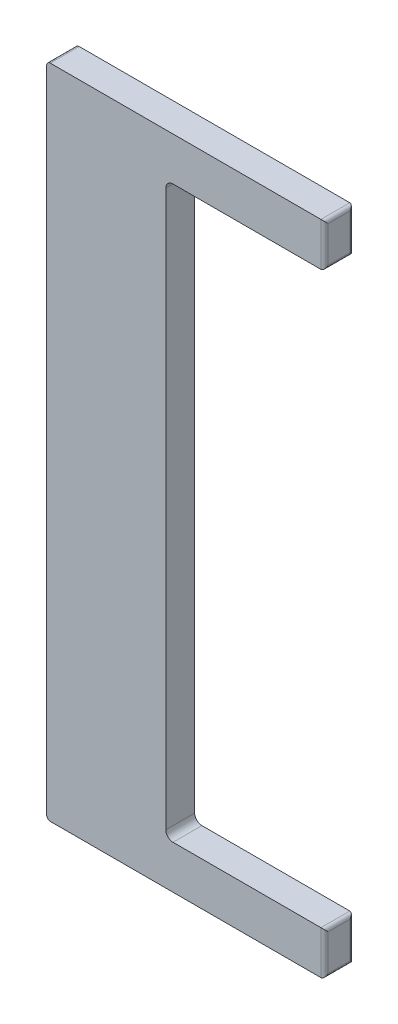
SolidWorks part; units mm, degrees
material "POLYURETHANE (11671)"
ref_plane "Front Plane" through (0, 0, 0) normal (0, 0, 1) x (1, 0, 0)
ref_plane "Top Plane" through (0, 0, 0) normal (0, 1, 0) x (1, 0, 0)
ref_plane "Right Plane" through (0, 0, 0) normal (1, 0, 0) x (0, 0, -1)
sketch "Sketch1" plane through (0, 0, 0) normal (0, 0, 1) x (1, 0, 0)
  line L0 (977.9, -152.4) -> (419.1, -152.4)
  line L1 (0, 0) -> (977.9, 0)
  line L2 (0, 0) -> (0, -2311.4)
  line L3 (0, -2311.4) -> (977.9, -2311.4)
  line L4 (977.9, 0) -> (977.9, -152.4)
  line L5 (419.1, -152.4) -> (419.1, -2159)
  line L6 (419.1, -2159) -> (977.9, -2159)
  line L7 (977.9, -2159) -> (977.9, -2311.4)
  dimension "D1" = 2311.4
  dimension "D2" = 977.9
  dimension "D3" = 152.4
  dimension "D4" = 152.4
  dimension "D5" = 419.1
extrude "Boss-Extrude1" add sketch "Sketch1" along normal blind 101.6
fillet "Fillet1" radius 25.4 2 edges at (419.1, -2159, 50.8) (419.1, -152.4, 50.8)
fillet "Fillet2" radius 12.7 10 edges at (977.9, -76.2, 0) (977.9, -76.2, 101.6) (977.9, -2235.2, 0) (977.9, -2235.2, 101.6) (977.9, -152.4, 50.8) (977.9, 0, 50.8) (0, 0, 50.8) (0, -2311.4, 50.8) (977.9, -2311.4, 50.8) (977.9, -2159, 50.8)
ref_plane "Plane1" through (0, -1155.7, 0) normal (0, 1, 0) x (1, 0, 0)
